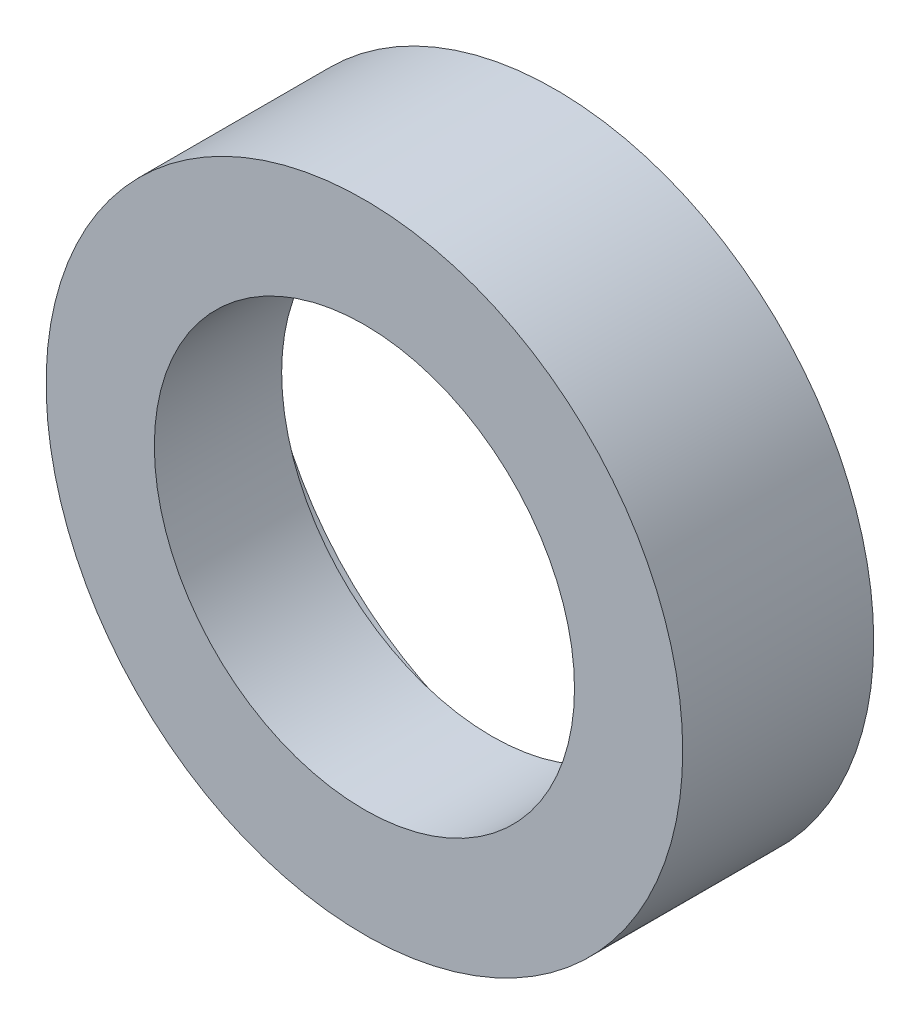
SolidWorks part; units mm, degrees
ref_plane "Front Plane" through (0, 0, 0) normal (0, 0, 1) x (1, 0, 0)
ref_plane "Top Plane" through (0, 0, 0) normal (0, 1, 0) x (1, 0, 0)
ref_plane "Right Plane" through (0, 0, 0) normal (1, 0, 0) x (0, 0, -1)
sketch "Sketch1" plane through (0, 0, 0) normal (0, 0, 1) x (1, 0, 0)
  circle A0 centre (0, 0) radius 46
  circle A1 centre (0, 0) radius 50
extrude "Boss-Extrude1" add sketch "Sketch1" along normal blind 10
sketch "Sketch2" plane through (0, 0, 10) normal (0, 0, 1) x (1, 0, 0)
  circle A0 centre (0, 0) radius 50
  circle A1 centre (0, 0) radius 33
extrude "Boss-Extrude2" add sketch "Sketch2" along normal blind 20
